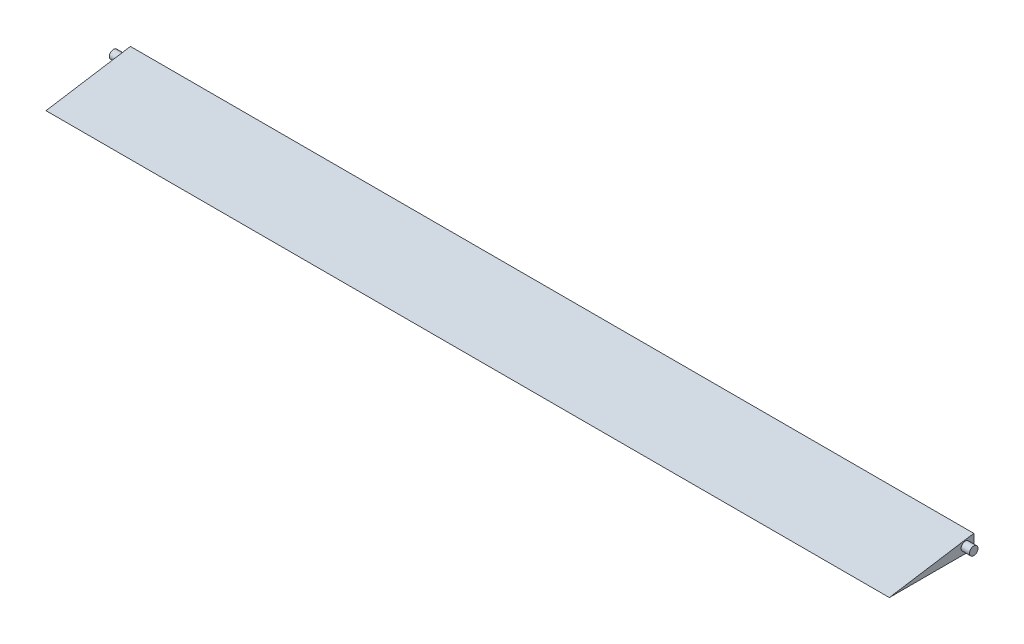
SolidWorks part; units mm, degrees
ref_plane "Ön Düzlem" through (0, 0, 0) normal (0, 0, 1) x (1, 0, 0)
ref_plane "Üst Düzlem" through (0, 0, 0) normal (0, 1, 0) x (1, 0, 0)
ref_plane "Sağ Düzlem" through (0, 0, 0) normal (1, 0, 0) x (0, 0, -1)
sketch "Çizim2" plane through (0, 0, 0) normal (1, 0, 0) x (0, 0, -1)
  line L0 (-25, 0) -> (25, 0)
  line L1 (25, 0) -> (25, 7.96)
  line L2 (-25, 0) -> (25, 7.96)
  point P2 (0, 0)
  dimension "D1" = 50
  dimension "D2" = 7.96
extrude "Yükseklik-Ekstrüzyon2" add sketch "Çizim2" along normal blind 499.5
sketch "Çizim4" plane through (499.5, 0, 0) normal (1, 0, 0) x (0, 0, -1)
  line L0 (25, 3.98) -> (20, 3.98) construction
  line L1 (25, 0) -> (25, 7.96) construction
  circle A0 centre (20, 3.98) radius 2.5
  dimension "D2" = 5
  dimension "D1" = 5
extrude "Yükseklik-Ekstrüzyon3" add sketch "Çizim4" along normal blind 5
sketch "Çizim5" plane through (0, 0, 0) normal (-1, 0, 0) x (0, 0, 1)
  line L0 (-25, 3.98) -> (-20, 3.98) construction
  line L1 (-25, 0) -> (-25, 7.96) construction
  circle A0 centre (-20, 3.98) radius 2.5
  dimension "D2" = 5
  dimension "D1" = 5
extrude "Yükseklik-Ekstrüzyon4" add sketch "Çizim5" along normal blind 5
